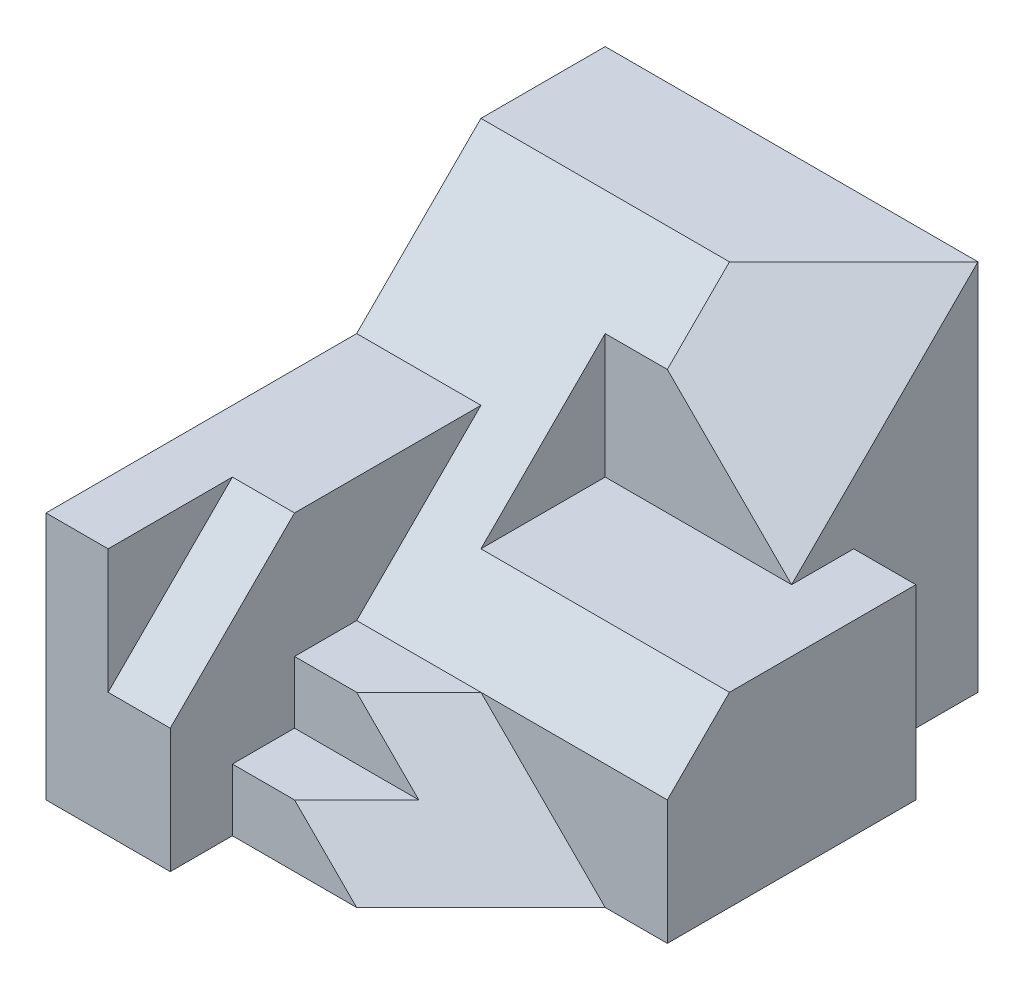
SolidWorks part; units mm, degrees
ref_plane "Front Plane" through (0, 0, 0) normal (0, 0, 1) x (1, 0, 0)
ref_plane "Top Plane" through (0, 0, 0) normal (0, 1, 0) x (1, 0, 0)
ref_plane "Right Plane" through (0, 0, 0) normal (1, 0, 0) x (0, 0, -1)
sketch "Sketch1" plane through (0, 0, 0) normal (0, 0, 1) x (1, 0, 0)
  line L1 (3.5, -3) -> (-3.5, -3)
  line L2 (3.5, -3) -> (3.5, 3)
  line L3 (3.5, 3) -> (-3.5, 3)
  line L4 (-3.5, -3) -> (-3.5, 3)
  line L5 (3.5, -3) -> (-3.5, 3) construction
  line L6 (3.5, 3) -> (-3.5, -3) construction
  point P0 (0, 0)
  dimension "D1" = 7
  dimension "D2" = 6
extrude "Boss-Extrude1" add sketch "Sketch1" along normal blind 9
sketch "Sketch2" plane through (-3.5, 0, 0) normal (-1, 0, 0) x (0, 0, 1)
  line L0 (2, 3) -> (4, 1)
  line L1 (9, 3) -> (0, 3) construction
  line L2 (4, 1) -> (9, 1)
  line L3 (9, 3) -> (9, -3) construction
  line L4 (9, 1) -> (9, 3)
  line L5 (9, 3) -> (2, 3)
  dimension "D1" = 2
  dimension "D2" = 5
  dimension "D3" = 2
extrude "Cut-Extrude1" cut sketch "Sketch2" against normal blind 2
sketch "Sketch3" plane through (3.5, 0, 0) normal (1, 0, 0) x (0, 0, -1)
  line L0 (0, -3) -> (-2, -3)
  line L1 (-9, -3) -> (0, -3) construction
  line L2 (-2, -3) -> (-2, 0)
  line L3 (-2, 0) -> (-3, 0)
  line L4 (-3, 0) -> (0, 3)
  line L5 (0, 3) -> (0, -3)
  dimension "D1" = 2
  dimension "D2" = 1
  dimension "D3" = 3
extrude "Cut-Extrude2" cut sketch "Sketch3" against normal blind 1
sketch "Sketch4" plane through (2.5, 0, 0) normal (1, 0, 0) x (0, 0, -1)
  line L0 (0, 3) -> (-3, 0)
sketch "Sketch5" plane through (-1.5, 0, 0) normal (-1, 0, 0) x (0, 0, 1)
  line L0 (2, 3) -> (4, 1)
  line L1 (4, 1) -> (9, 1)
  line L2 (9, 1) -> (9, 3)
  line L3 (9, 3) -> (2, 3)
extrude "Cut-Extrude3" cut sketch "Sketch5" against normal through all
sketch "Sketch6" plane through (0, 2.5, 2.5) normal (0, 0.7071, 0.7071) x (1, 0, 0)
  line L0 (0.5, 0.7071) -> (0.5, -0.1213)
  line L1 (3.5, 0.7071) -> (-3.5, 0.7071) construction
  line L2 (-3.5, 0.7071) -> (-3.5, -2.1213) construction
  line L3 (3.5, -2.1213) -> (-3.5, -2.1213) construction
  dimension "D1" = 4
  dimension "D2" = 2
ref_plane "Plane1" through (1.8333, 1.8333, 1.8333) normal (0.5774, 0.5774, 0.5774) x (0.8165, -0.4082, -0.4082)
sketch "Sketch8" plane through (0, 3, 0) normal (0, 1, 0) x (1, 0, 0)
  line L0 (3.5, 0) -> (2.5, 0)
  line L1 (2.5, 0) -> (2.5, -4)
  line L2 (2.5, -4) -> (3.5, -4)
  line L3 (3.5, -4) -> (3.5, 0)
  line L4 (3.5, -4) -> (-3.5, -4) construction
extrude "Cut-Extrude6" cut sketch "Sketch8" against normal blind 2
sketch "Sketch9" plane through (3.5, 0, 0) normal (1, 0, 0) x (0, 0, -1)
  line L0 (-2, 1) -> (-3, 0)
  line L1 (-3, 0) -> (-2, 0) construction
  line L2 (-2, 1) -> (-3, 0) construction
  line L3 (-3, 0) -> (-5, 0)
  line L4 (-5, 0) -> (-5, 1)
  line L5 (-2, 1) -> (-9, 1) construction
  line L6 (-5, 1) -> (-2, 1)
  dimension "D1" = 3
extrude "Cut-Extrude7" cut sketch "Sketch9" against normal blind 1
sketch "Sketch11" plane through (3.5, 0, 0) normal (1, 0, 0) x (0, 0, -1)
  line L0 (-4, 1) -> (-4, 0)
  line L1 (-5, 0) -> (-2, 0) construction
  line L2 (-4, 0) -> (-6, 0)
  line L3 (-6, 0) -> (-6, 1)
  line L4 (-5, 1) -> (-9, 1) construction
  line L5 (-6, 1) -> (-4, 1)
  dimension "D1" = 2
extrude "Cut-Extrude9" cut sketch "Sketch11" against normal blind 3
sketch "Sketch13" plane through (2.5, 0, 0) normal (1, 0, 0) x (0, 0, -1)
  line L0 (-5, 0) -> (-3, 0)
  line L1 (-6, 0) -> (-4, 0) construction
  line L2 (-3, 0) -> (-3, 2)
  line L3 (-4, 1) -> (-2, 3) construction
  line L4 (-3, 2) -> (-5, 0)
extrude "Cut-Extrude11" cut sketch "Sketch13" against normal blind 3
sketch "Sketch14" plane through (0.5, 0, 0) normal (1, 0, 0) x (0, 0, -1)
  line L0 (-4, 1) -> (-5, 0)
  line L1 (-5, 0) -> (-6, 0)
  line L2 (-6, 0) -> (-6, 1)
  line L3 (-6, 1) -> (-4, 1)
extrude "Cut-Extrude12" cut sketch "Sketch14" against normal blind 1
sketch "Sketch15" plane through (3.5, 0, 0) normal (1, 0, 0) x (0, 0, -1)
  line L0 (-7, 1) -> (-9, -1)
  line L1 (-6, 1) -> (-9, 1) construction
  line L2 (-9, -3) -> (-9, 1) construction
  line L3 (-9, -1) -> (-9, 1)
  line L4 (-9, 1) -> (-7, 1)
  dimension "D1" = 2
  dimension "D2" = 2
extrude "Cut-Extrude13" cut sketch "Sketch15" against normal blind 6
sketch "Sketch17" plane through (3.5, 0, 0) normal (1, 0, 0) x (0, 0, -1)
  line L0 (-5, 0) -> (-6, 0)
  line L1 (-6, 0) -> (-6, 1)
  line L2 (-5, 0) -> (-6, -1)
  line L3 (-6, -1) -> (-6, -3)
  line L4 (-9, -3) -> (-2, -3) construction
  line L5 (-6, 1) -> (-7, 1)
  line L7 (-7, 1) -> (-9, -1)
  line L8 (-9, -1) -> (-9, -3)
  line L9 (-9, -3) -> (-6, -3)
  dimension "D1" = 3
  dimension "D2" = 2
extrude "Cut-Extrude14" cut sketch "Sketch17" against normal blind 5
sketch "Sketch18" plane through (3.5, 0, 0) normal (1, 0, 0) x (0, 0, -1)
  line L0 (-3, 2) -> (-5, 0)
  line L1 (-5, 0) -> (-6, 0)
  line L2 (-6, 0) -> (-6, 1)
  line L3 (-6, 1) -> (-3, 2)
extrude "Cut-Extrude16" cut sketch "Sketch18" against normal blind 5
ref_plane "Plane4" through (1.8333, 1.8333, 1.8333) normal (0.5774, 0.5774, 0.5774) x (0.8165, -0.4082, -0.4082)
sketch "Sketch20" plane through (1.8333, 1.8333, 1.8333) normal (0.5774, 0.5774, 0.5774) x (0.8165, -0.4082, -0.4082)
  line L0 (-1.633, 0.7071) -> (-1.633, -0.7071)
  line L1 (-2.4495, -0.7071) -> (0, -0.7071) construction
  line L2 (-1.633, -0.7071) -> (0.8165, -2.1213)
  line L3 (0.8165, -2.1213) -> (0.8165, 2.1213)
  line L4 (0.8165, 2.1213) -> (-1.633, 0.7071)
extrude "Cut-Extrude17" cut sketch "Sketch20" along normal through all
sketch "Sketch21" plane through (-1.5, 0, 0) normal (1, 0, 0) x (0, 0, -1)
  line L0 (-6, -1) -> (-7, -1)
  line L1 (-7, -1) -> (-7, -2)
  line L2 (-7, -2) -> (-8, -2)
  line L3 (-8, -2) -> (-8, -3)
  line L4 (-9, -3) -> (-6, -3) construction
  line L5 (-8, -3) -> (-6, -3)
  line L6 (-6, -3) -> (-6, -1)
  dimension "D1" = 1
  dimension "D2" = 1
  dimension "D3" = 1
  dimension "D4" = 1
extrude "Boss-Extrude2" add sketch "Sketch21" along normal blind 4
sketch "Sketch22" plane through (0, -1, 0) normal (0, 1, 0) x (1, 0, 0)
  line L0 (0.5, -6) -> (-0.5, -7)
  line L1 (-1.5, -6) -> (2.5, -6) construction
  line L2 (2.5, -7) -> (-1.5, -7) construction
  dimension "D1" = 2
  dimension "D2" = 1
sketch "Sketch23" plane through (0, -3, 0) normal (0, -1, 0) x (1, 0, 0)
  line L0 (2.5, 6) -> (0.5, 8)
  line L1 (2.5, 8) -> (-1.5, 8) construction
  dimension "D1" = 2
ref_plane "Plane5" through (1.8333, 1.8333, 1.8333) normal (0.5774, 0.5774, 0.5774) x (0.8165, -0.4082, -0.4082)
sketch "Sketch24" plane through (1.8333, 1.8333, 1.8333) normal (0.5774, 0.5774, 0.5774) x (0.8165, -0.4082, -0.4082)
  line L0 (0.8165, -6.364) -> (-1.633, -4.9497)
  line L1 (0.8165, -6.364) -> (-1.633, -7.7782)
  line L2 (-1.633, -7.7782) -> (-2.8577, -5.6569)
  line L3 (-2.8577, -5.6569) -> (-1.633, -4.9497)
extrude "Cut-Extrude19" cut sketch "Sketch24" along normal blind 4
sketch "Sketch25" plane through (0, -1, 0) normal (0, 1, 0) x (1, 0, 0)
  line L0 (2.5, -6) -> (0.5, -8)
  line L1 (0.5, -8) -> (2.5, -8)
  line L2 (2.5, -8) -> (2.5, -6)
extrude "Cut-Extrude20" cut sketch "Sketch25" against normal through all
sketch "Sketch26" plane through (1.8333, 1.8333, 1.8333) normal (0.5774, 0.5774, 0.5774) x (0.8165, -0.4082, -0.4082)
  line L0 (-1.633, -6.364) -> (-2.8577, -7.0711)
  line L1 (-2.8577, -7.0711) -> (-1.633, -7.7782)
  line L2 (-1.633, -7.7782) -> (-1.633, -6.364)
  line L3 (-2.0412, -7.0711) -> (-3.6742, -7.0711) construction
  line L4 (-1.633, -6.364) -> (-2.2454, -6.7175) construction
extrude "Cut-Extrude22" cut sketch "Sketch26" along normal through all
sketch "Sketch27" plane through (1.8333, 1.8333, 1.8333) normal (0.5774, 0.5774, 0.5774) x (0.8165, -0.4082, -0.4082)
  line L6 (-1.633, -4.9497) -> (-1.6403, -4.9365)
sketch "Sketch28" plane through (0, 0, 6) normal (0, 0, 1) x (1, 0, 0)
  line L0 (2.5, -3) -> (0.5, -1)
  line L1 (0.5, -1) -> (2.5, -1)
  line L2 (2.5, -1) -> (2.5, -3)
  line L3 (2.5, -3) -> (2.4973, -3.0103)
  line M2 (2.5, -1) -> (2.5, -3)
extrude "Cut-Extrude23" cut sketch "Sketch28" along normal blind 10 contours L1 L0 M2
